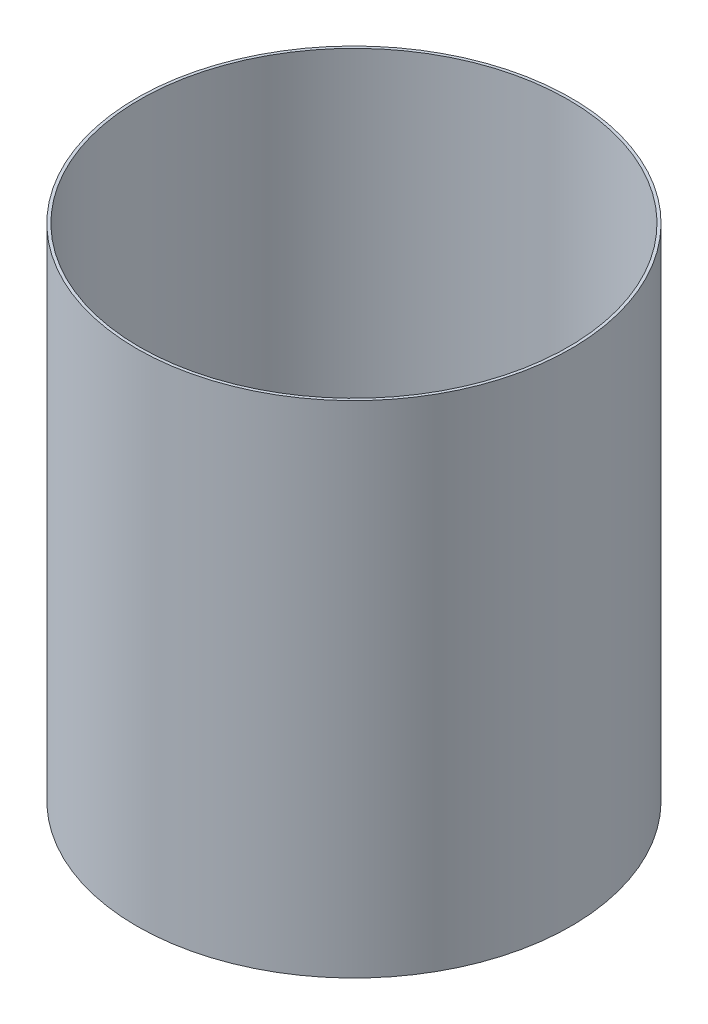
SolidWorks part; units mm, degrees
material "PTFE (general)"
ref_plane "Front Plane" through (0, 0, 0) normal (0, 0, 1) x (1, 0, 0)
ref_plane "Top Plane" through (0, 0, 0) normal (0, 1, 0) x (1, 0, 0)
ref_plane "Right Plane" through (0, 0, 0) normal (1, 0, 0) x (0, 0, -1)
ref_axis "Axis1" through (0, 55, 0) along (0, -1, 0)
sketch "Sketch2" plane through (0, 0, 0) normal (0, 0, 1) x (1, 0, 0)
  line L0 (0, 55) -> (0, -55) construction
  line L1 (76.2, 86.1492) -> (77.216, 86.1492)
  line L2 (76.2, 86.1492) -> (76.2, -91.6508)
  line L3 (76.2, -91.6508) -> (77.216, -91.6508)
  line L4 (77.216, 86.1492) -> (77.216, -91.6508)
  dimension "D1" = 177.8
  dimension "D2" = 1.016
  dimension "D3" = 76.2
revolve "Revolve1" add sketch "Sketch2" angle 360 about axis through (0, 55, 0) along (0, -1, 0)
